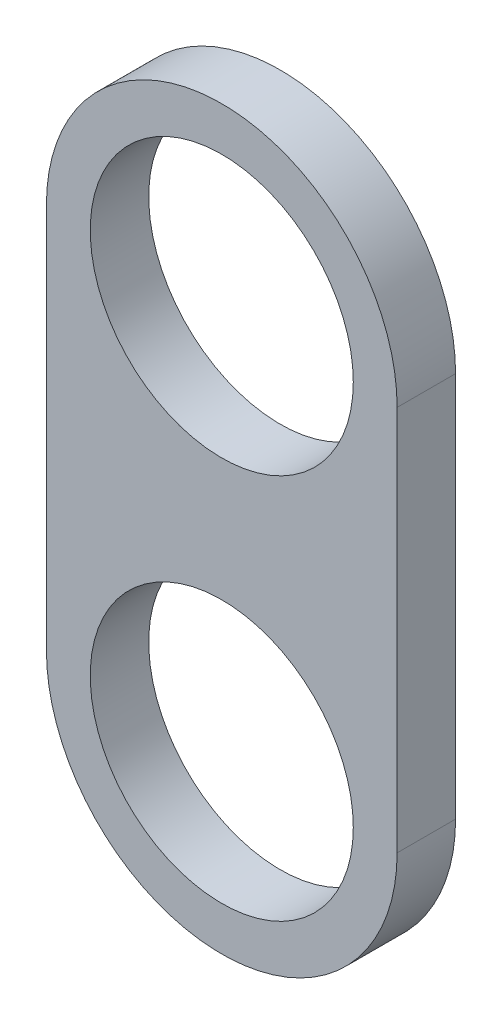
SolidWorks part; units mm, degrees
ref_plane "Front Plane" through (0, 0, 0) normal (0, 0, 1) x (1, 0, 0)
ref_plane "Top Plane" through (0, 0, 0) normal (0, 1, 0) x (1, 0, 0)
ref_plane "Right Plane" through (0, 0, 0) normal (1, 0, 0) x (0, 0, -1)
sketch "Sketch1" plane through (0, 0, 0) normal (0, 0, 1) x (1, 0, 0)
  line L0 (0, 0) -> (0, 41.91) construction
  line L1 (-19.05, 0) -> (-19.05, 41.91)
  line L2 (19.05, 0) -> (19.05, 41.91)
  arc A0 (-19.05, 0) -> (19.05, 0) centre (0, 0) ccw
  arc A1 (19.05, 41.91) -> (-19.05, 41.91) centre (0, 41.91) ccw
  point P3 (0, 20.955)
  dimension "D1" = 19.05
  dimension "D2" = 41.91
extrude "Boss-Extrude1" add sketch "Sketch1" along normal blind 6.35
hole_wizard "1 (1) Diameter Hole1" positions "Sketch2" profile "Sketch3" hole size "1" standard "ANSI Inch"
sketch "Sketch2" plane through (0, 0, 6.35) normal (0, 0, 1) x (1, 0, 0)
  arc A0 (19.05, 41.91) -> (-19.05, 41.91) centre (0, 41.91) ccw construction
  point P0 (0, 41.91)
  point P6 (0, 0)
sketch "Sketch3" plane through (0, 41.91, 6.35) normal (1, 0, 0) x (0, -1, 0)
  line L0 (0, 0) -> (0, 33.9848)
  line L1 (0, 33.9848) -> (14.2875, 25.4)
  line L2 (14.2875, 25.4) -> (14.2875, 0)
  line L5 (14.2875, 0) -> (0, 0)
  line L10 (0, 33.9848) -> (-14.2875, 25.4) construction
  line L11 (0, -6.35) -> (0, 107.95) construction
  dimension "Hole Dia." = 28.575
  dimension "Hole Depth" = 25.4
  dimension "Drill Angle" = 118
